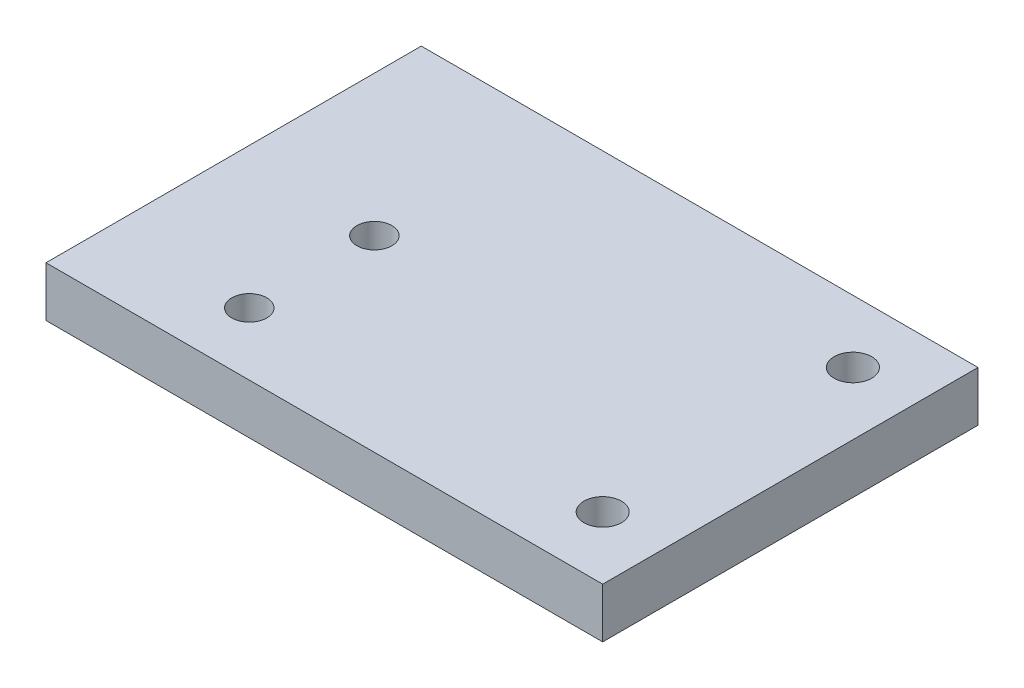
SolidWorks part; units mm, degrees
ref_plane "Front Plane" through (0, 0, 0) normal (0, 0, 1) x (1, 0, 0)
ref_plane "Top Plane" through (0, 0, 0) normal (0, 1, 0) x (1, 0, 0)
ref_plane "Right Plane" through (0, 0, 0) normal (1, 0, 0) x (0, 0, -1)
sketch "Sketch1" plane through (0, 0, 0) normal (0, 1, 0) x (1, 0, 0)
  line L1 (39.5, 25) -> (59.5, 25) construction
  line L2 (39.5, 25) -> (39.5, 5) construction
  line L3 (39.5, 5) -> (59.5, 5) construction
  line L4 (59.5, 25) -> (59.5, 5) construction
  line L5 (22.5, 30) -> (44.5, 30)
  line L6 (22.5, 30) -> (22.5, 0)
  line L7 (22.5, 0) -> (44.5, 0)
  line L8 (44.5, 30) -> (44.5, 0)
  line L9 (22.5, 0) -> (0, 0)
  line L10 (22.5, 0) -> (22.5, 30)
  line L11 (22.5, 30) -> (0, 30)
  line L12 (0, 0) -> (0, 30)
  circle A0 centre (39.5, 25) radius 1.5
  circle A1 centre (39.5, 5) radius 1.5
  circle A2 centre (11.25, 15) radius 1.4
  circle A3 centre (11.25, 5) radius 1.4
  point P16 (0, 0)
  point P18 (0, 0)
  dimension "D3" = 3
  dimension "D4" = 3
  dimension "D5" = 5
  dimension "D7" = 5
  dimension "D10" = 11.25
  dimension "D11" = 10
  dimension "D12" = 5
  dimension "D13" = 11.25
  dimension "D14" = 2.8
  dimension "D15" = 2.8
  dimension "D1" = 20
  dimension "D2" = 20
  dimension "D6" = 5
  dimension "D8" = 17
  dimension "D9" = 22.5
extrude "Boss-Extrude1" add sketch "Sketch1" along normal blind 4 contours L12 L9 L6 L11 A3 A2 | L8 L5 L6 L7 A1 A0
